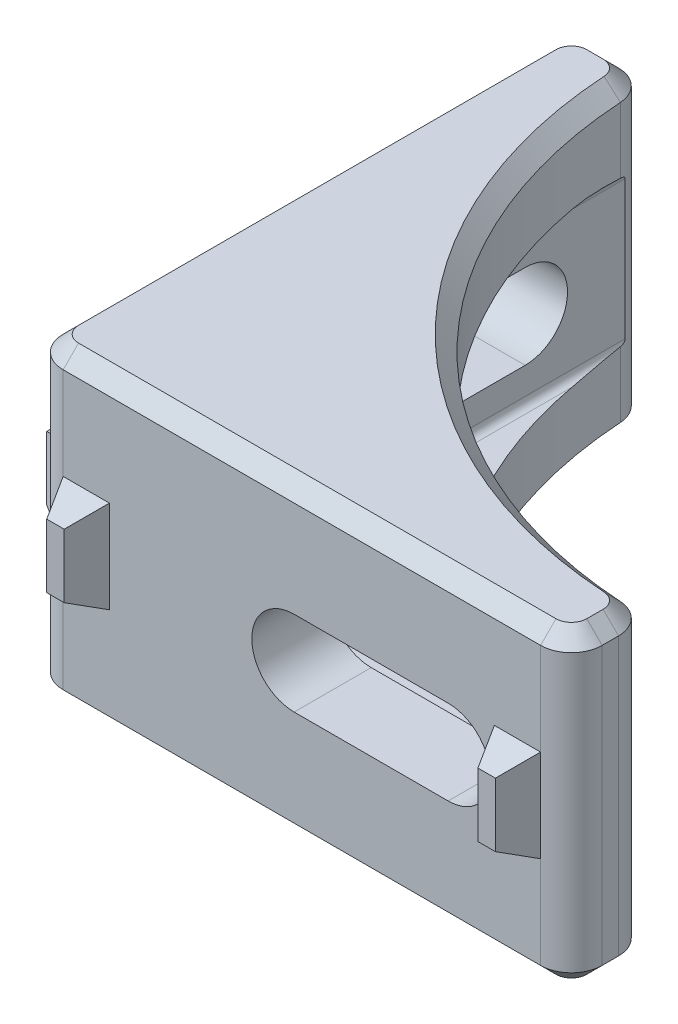
SolidWorks part; units mm, degrees
ref_plane "Front Plane" through (0, 0, 0) normal (0, 0, 1) x (1, 0, 0)
ref_plane "Top Plane" through (0, 0, 0) normal (0, 1, 0) x (1, 0, 0)
ref_plane "Right Plane" through (0, 0, 0) normal (1, 0, 0) x (0, 0, -1)
sketch "Sketch1" plane through (0, 0, 0) normal (0, 1, 0) x (1, 0, 0)
  line L0 (-17.5, 15.5) -> (-17.5, -15.5)
  line L1 (-15.5, -17.5) -> (15.5, -17.5)
  line L4 (-12.5, 17.5) -> (-12.5, -12.5) construction
  line L5 (-12.5, -12.5) -> (17.5, -12.5) construction
  line L6 (-14.4374, 17.5) -> (-15.5, 17.5)
  line L7 (17.5, -14.4374) -> (17.5, -15.5)
  arc A0 (-12.4413, 15.625) -> (15.625, -12.4413) centre (17.5, 17.5) ccw
  arc A1 (-17.5, 15.5) -> (-15.5, 17.5) centre (-15.5, 15.5) cw
  arc A2 (17.5, -14.4374) -> (15.625, -12.4413) centre (15.5, -14.4374) ccw
  arc A3 (15.5, -17.5) -> (17.5, -15.5) centre (15.5, -15.5) ccw
  arc A4 (-17.5, -15.5) -> (-15.5, -17.5) centre (-15.5, -15.5) ccw
  arc A5 (-14.4374, 17.5) -> (-12.4413, 15.625) centre (-14.4374, 15.5) cw
  point P3 (0, -17.5)
  point P5 (-17.5, 0)
  point P21 (17.5, -17.5)
  point P24 (-17.5, -17.5)
  dimension "D5" = 2
  dimension "D6" = 2
  dimension "D1" = 35
  dimension "D2" = 5
  dimension "D3" = 5
  dimension "D4" = 35
extrude "Boss-Extrude1" add sketch "Sketch1" along normal blind 20
sketch "Sketch3" plane through (0, 20, 0) normal (0, 1, 0) x (1, 0, 0)
  line L2 (-12.5, 33.24) -> (-12.5, -12.5)
  line L3 (-12.5, -12.5) -> (41.3053, -12.5)
  line L4 (41.3053, -12.5) -> (-12.5, 33.24)
  line L5 (-17.5, 15.5) -> (-17.5, -15.5) construction
  line L6 (-15.5, -17.5) -> (15.5, -17.5) construction
  dimension "D1" = 5
  dimension "D2" = 5
extrude "Cut-Extrude2" cut sketch "Sketch3" against normal mid plane 10 from offset 10 offset against normal yes
sketch "Sketch2" plane through (-17.5, 0, 0) normal (-1, 0, 0) x (0, 0, 1)
  line L0 (-17.5, 10) -> (17.5, 10) construction
  line L1 (-17.5, 20) -> (-17.5, 0) construction
  line L2 (17.5, 20) -> (17.5, 0) construction
  line L3 (-9.5, 10) -> (0.5, 10) construction
  line L4 (-9.5, 12.75) -> (0.5, 12.75)
  line L5 (-9.5, 7.25) -> (0.5, 7.25)
  arc A0 (-9.5, 12.75) -> (-9.5, 7.25) centre (-9.5, 10) ccw
  arc A1 (0.5, 7.25) -> (0.5, 12.75) centre (0.5, 10) ccw
  point P8 (-4.5, 10)
  dimension "D1" = 10
  dimension "D2" = 5.5
  dimension "D3" = 8
extrude "Cut-Extrude1" cut sketch "Sketch2" against normal through all both and the other way through all
sketch "Sketch5" plane through (-17.5, 0, 0) normal (-1, 0, 0) x (0, 0, 1)
  line L0 (-21.994, 10) -> (25.022, 10) construction
  line L1 (-17.5, 20) -> (-17.5, 0) construction
  line L2 (-12.5, 13) -> (-15.5, 13)
  line L3 (-12.5, 13) -> (-12.5, 7)
  line L4 (-12.5, 7) -> (-15.5, 7)
  line L5 (-15.5, 13) -> (-15.5, 7)
  line L6 (-12.5, 13) -> (-15.5, 7) construction
  line L7 (-12.5, 7) -> (-15.5, 13) construction
  line L8 (0, 0) -> (0, 32.7455) construction
  line L9 (12.5, 13) -> (15.5, 7) construction
  line L10 (12.5, 7) -> (15.5, 13) construction
  line L11 (12.5, 13) -> (12.5, 7)
  line L12 (12.5, 7) -> (15.5, 7)
  line L13 (15.5, 13) -> (15.5, 7)
  line L14 (12.5, 13) -> (15.5, 13)
  point P3 (-14, 10)
  dimension "D1" = 6
  dimension "D2" = 3
  dimension "D3" = 2
extrude "Boss-Extrude2" add sketch "Sketch5" along normal blind 2 draft 25
ref_plane "Plane1" through (0, 0, 0) normal (0.7071, 0, 0.7071) x (0, -1, 0)
mirror "Mirror1" about plane through (0, 0, 0) normal (0.7071, 0, 0.7071) of "Cut-Extrude1", "Boss-Extrude2"
fillet "Fillet1" radius 8 1 edges at (-12.5, 10, 12.5)
chamfer "Chamfer1" [suppressed] distance 1 angle 45
chamfer "Chamfer2" distance 1 angle 45 20 edges at (-17.5, 0, 0) (-16.9142, 0, 16.9142) (0, 0, 17.5) (16.9142, 0, 16.9142) (17.5, 0, 14.9687) (16.9577, 0, 13.0681) (-3.7132, 0, 3.7132) (-13.0681, 0, -16.9577) (-14.9687, 0, -17.5) (-16.9142, 0, -16.9142) (-14.9687, 20, -17.5) (-13.0681, 20, -16.9577) (-3.7132, 20, 3.7132) (16.9577, 20, 13.0681) (17.5, 20, 14.9687) (16.9142, 20, 16.9142) (0, 20, 17.5) (-16.9142, 20, 16.9142) (-17.5, 20, 0) (-16.9142, 20, -16.9142)
fillet "Fillet2" radius 0.5 6 edges at (5.7482, 5, 12.5) (-10.1569, 5, 10.1569) (5.7482, 15, 12.5) (-10.1569, 15, 10.1569) (-12.5, 5, -5.7482) (-12.5, 15, -5.7482)
